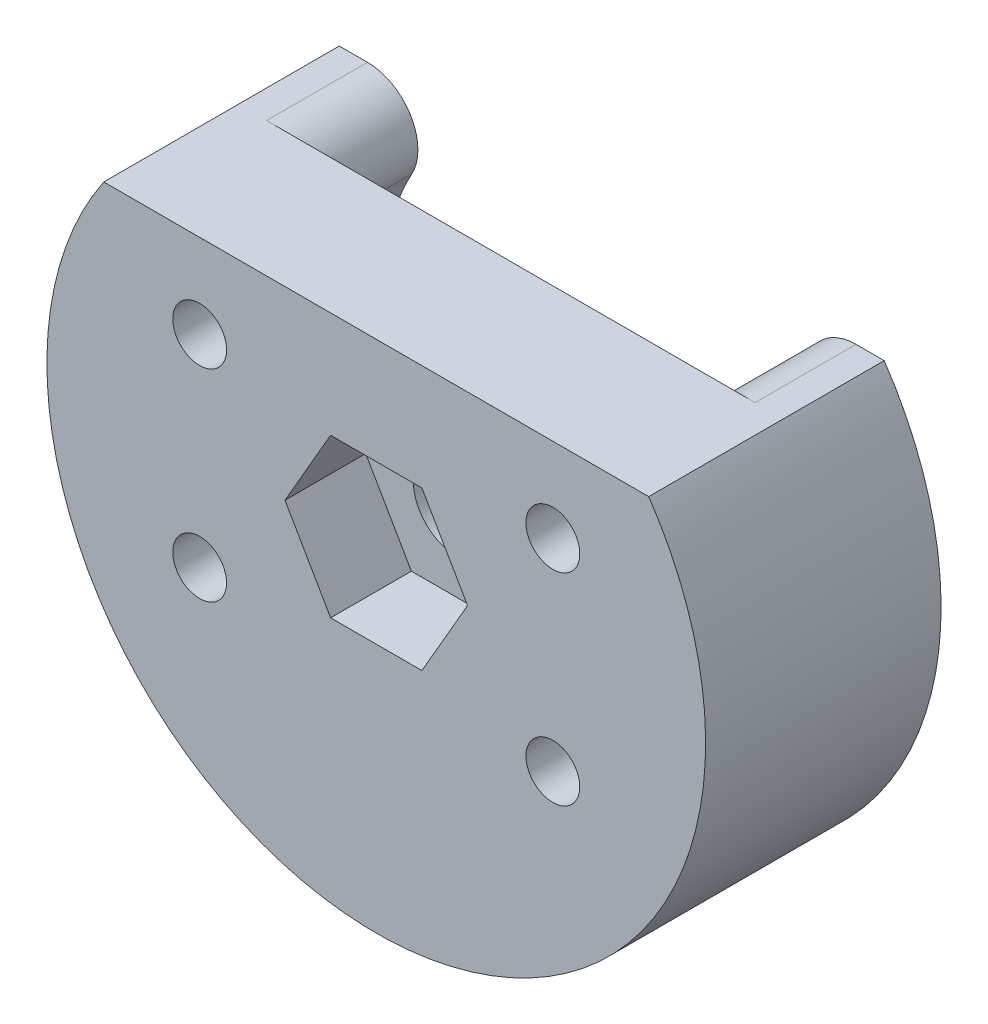
SolidWorks part; units mm, degrees
ref_plane "Front Plane" through (0, 0, 0) normal (0, 0, 1) x (1, 0, 0)
ref_plane "Top Plane" through (0, 0, 0) normal (0, 1, 0) x (1, 0, 0)
ref_plane "Right Plane" through (0, 0, 0) normal (1, 0, 0) x (0, 0, -1)
sketch "Sketch1" plane through (0, 0, 0) normal (0, 0, 1) x (1, 0, 0)
  line L0 (0, 0) -> (0, 12.5) construction
  line L1 (16.2, 12.5) -> (16.2, 0) construction
  line L2 (0, 0) -> (16.2, 0) construction
  line L3 (0, 12.5) -> (16.2, 12.5)
  line L4 (2.85, 4) -> (13.35, 10) construction
  arc A0 (0, 12.5) -> (16.2, 12.5) centre (8.1, 7) ccw
  circle A4 centre (2.85, 10) radius 0.8
  circle A5 centre (13.35, 10) radius 0.8
  circle A6 centre (13.35, 4) radius 0.8
  circle A7 centre (2.85, 4) radius 0.8
  point P1 (8.1, -2.7908)
  dimension "D11" = 1.6
  dimension "D1" = 2.85
  dimension "D2" = 4
  dimension "D3" = 4
  dimension "D4" = 2.85
  dimension "D5" = 6
  dimension "D6" = 6
  dimension "D7" = 2.85
  dimension "D8" = 2.85
  dimension "D9" = 2.5
  dimension "D10" = 15.2908
extrude "Boss-Extrude1" add sketch "Sketch1" along normal blind 4
sketch "Sketch2" plane through (0, 0, 4) normal (0, 0, 1) x (1, 0, 0)
  line L0 (2.85, 10) -> (13.35, 4) construction
  line L1 (2.85, 4) -> (13.35, 10) construction
  line L2 (10.8135, 7) -> (9.4568, 9.35)
  line L3 (9.4568, 9.35) -> (6.7432, 9.35)
  line L4 (6.7432, 9.35) -> (5.3865, 7)
  line L5 (5.3865, 7) -> (6.7432, 4.65)
  line L6 (6.7432, 4.65) -> (9.4568, 4.65)
  line L7 (9.4568, 4.65) -> (10.8135, 7)
  circle A1 centre (8.1, 7) radius 2.35 construction
  dimension "D2" = 4.7
extrude "Cut-Extrude1" cut sketch "Sketch2" against normal blind 2.4
sketch "Sketch3" plane through (0, 0, 4) normal (0, 0, 1) x (1, 0, 0)
  line L0 (2.85, 10) -> (13.35, 4) construction
  circle A0 centre (8.1, 7) radius 1.3
  dimension "D1" = 2.6
extrude "Cut-Extrude2" cut sketch "Sketch3" against normal up to surface (4 mm away) up to face at (8.1, 4.8546, 0)
sketch "Sketch4" plane through (0, 0, 0) normal (0, 0, 1) x (1, 0, 0)
  line L0 (16.2, 12.5) -> (0, 12.5) construction
  line L1 (8.1, 12.5) -> (8.1, 7) construction
  line L2 (16.2, 12.5) -> (0, 12.5) construction
  line L3 (16.2, 12.5) -> (15.3621, 12.5)
  line L4 (1.69, 9.242) -> (-1.4307, 9.242) construction
  line L5 (2.85, 4) -> (8.1, 7) construction
  line L6 (2.2039, 3.6308) -> (-0.4008, 2.1424) construction
  line L7 (0, 12.5) -> (0.8379, 12.5)
  arc A0 (15.3621, 12.5) -> (14.0482, 10.2763) centre (15.3621, 11) ccw
  arc A1 (0, 12.5) -> (16.2, 12.5) centre (8.1, 7) ccw construction
  arc A2 (0.8379, 12.5) -> (2.1518, 10.2763) centre (0.8379, 11) cw
  arc A3 (2.1518, 10.2763) -> (14.0482, 10.2763) centre (8.1, 7) ccw
  arc A4 (0, 12.5) -> (16.2, 12.5) centre (8.1, 7) ccw
extrude "Boss-Extrude2" add sketch "Sketch4" against normal blind 3
